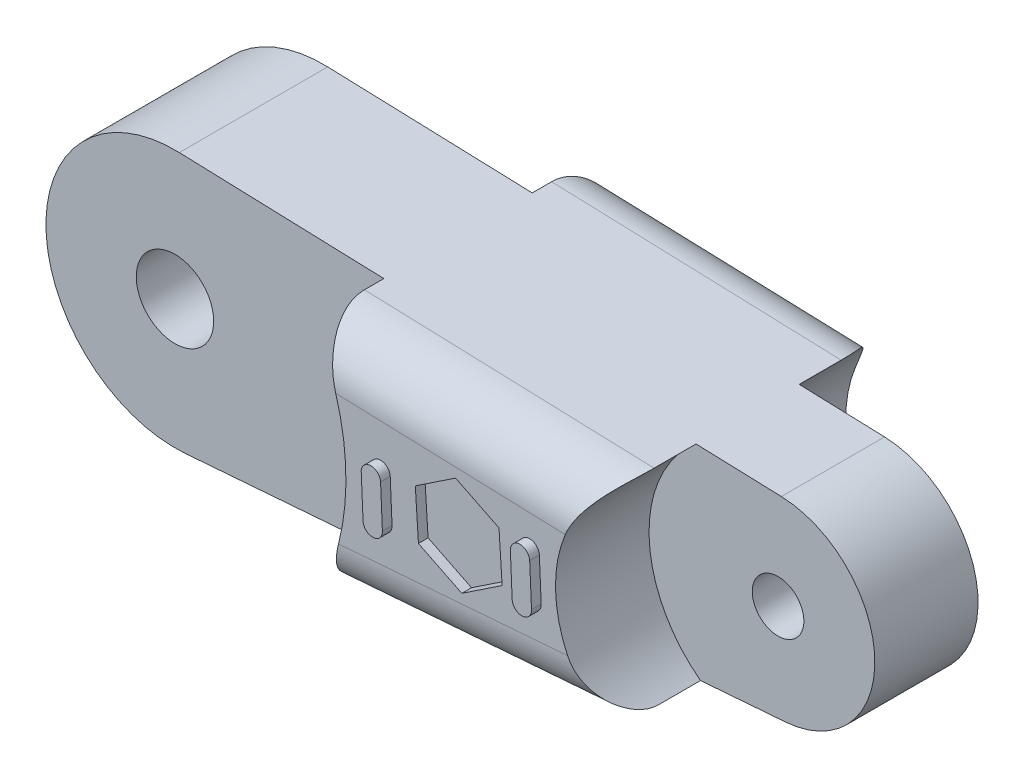
SolidWorks part; units mm, degrees
ref_plane "Front Plane" through (0, 0, 0) normal (0, 0, 1) x (1, 0, 0)
ref_plane "Top Plane" through (0, 0, 0) normal (0, 1, 0) x (1, 0, 0)
ref_plane "Right Plane" through (0, 0, 0) normal (1, 0, 0) x (0, 0, -1)
sketch "Sketch1" plane through (0, 0, 0) normal (0, 1, 0) x (1, 0, 0)
  line L0 (-91.1353, -13.0139) -> (-1.5416, -19.9405)
  line L1 (-90.4891, 16.9328) -> (-0.6801, 19.9884)
  arc A0 (-1.5416, -19.9405) -> (-0.6801, 19.9884) centre (0, 0) ccw
  arc A1 (-90.4891, 16.9328) -> (-91.1353, -13.0139) centre (-89.9791, 1.9414) ccw
  dimension "D2" = 30
  dimension "D3" = 40
  dimension "D1" = 90
extrude "Boss-Extrude1" add sketch "Sketch1" along normal mid plane 45
sketch "Sketch2" plane through (0, -22.5, 0) normal (0, -1, 0) x (1, 0, 0)
  circle A0 centre (0, 0) radius 37.5
  circle A1 centre (-89.9791, -1.9414) radius 20
  dimension "D1" = 40
  dimension "D2" = 75
extrude "Cut-Extrude1" cut sketch "Sketch2" against normal blind 11
ref_plane "Plane1" through (0, 0, 0) normal (0, -1, 0) x (-1, 0, 0)
mirror "Mirror1" about plane through (0, 0, 0) normal (0, -1, 0) of "Cut-Extrude1"
fillet "Fillet1" radius 8 4 edges at (-55.5573, 22.5, 15.7645) (-54.8256, 22.5, -18.1462) (-54.8256, -22.5, -18.1462) (-55.5573, -22.5, 15.7645)
sketch "Sketch4" plane through (0, -11.5, 0) normal (0, -1, 0) x (1, 0, 0)
  circle A0 centre (0, 0) radius 6
  circle A1 centre (-89.9791, -1.9414) radius 4
  dimension "D1" = 12
  dimension "D2" = 8
extrude "Cut-Extrude2" cut sketch "Sketch4" against normal blind 40
sketch "Sketch5" plane through (0, 22.5, 0) normal (0, 1, 0) x (1, 0, 0)
  line L0 (-89.9791, 1.9414) -> (0, 0) construction
  line L2 (-61.5566, 4.8014) -> (-61.3986, -2.7025)
  line L3 (-61.3986, -2.7025) -> (-54.821, -6.3176)
  line L4 (-54.821, -6.3176) -> (-48.4015, -2.4288)
  line L5 (-48.4015, -2.4288) -> (-48.5595, 5.0751)
  line L6 (-48.5595, 5.0751) -> (-55.1371, 8.6902)
  line L7 (-55.1371, 8.6902) -> (-61.5566, 4.8014)
  circle A0 centre (-54.9791, 1.1863) radius 6.5 construction
  point P0 (-89.9791, 1.9414)
  point P1 (0, 0)
  point P9 (-48.4805, 1.3231)
  dimension "D1" = 13
  dimension "D2" = 35
extrude "Cut-Extrude3" cut sketch "Sketch5" against normal blind 1.5
sketch "Sketch6" plane through (0, 22.5, 0) normal (0, 1, 0) x (1, 0, 0)
  line L0 (-89.9791, 1.9414) -> (0, 0) construction
  line L1 (-66.1277, -1.9195) -> (-66.1277, 4.5371) construction
  line L2 (-67.6277, -1.9195) -> (-67.6277, 4.5371)
  line L3 (-64.6277, -1.9195) -> (-64.6277, 4.5371)
  line L4 (-42.9913, -1.9195) -> (-42.9913, 4.5371) construction
  line L5 (-44.4913, -1.9195) -> (-44.4913, 4.5371)
  line L6 (-41.4913, -1.9195) -> (-41.4913, 4.5371)
  arc A0 (-77.9459, -14.0336) -> (-77.268, 17.3826) centre (-89.9791, 1.9414) ccw construction
  arc A1 (-35.9157, 10.7849) -> (-36.3474, -9.2258) centre (0, 0) ccw construction
  arc A2 (-67.6277, -1.9195) -> (-64.6277, -1.9195) centre (-66.1277, -1.9195) ccw
  arc A3 (-64.6277, 4.5371) -> (-67.6277, 4.5371) centre (-66.1277, 4.5371) ccw
  arc A4 (-44.4913, -1.9195) -> (-41.4913, -1.9195) centre (-42.9913, -1.9195) ccw
  arc A5 (-41.4913, 4.5371) -> (-44.4913, 4.5371) centre (-42.9913, 4.5371) ccw
  point P0 (-89.9791, 1.9414)
  point P1 (0, 0)
  point P7 (-69.9837, 1.51)
  point P8 (-61.4837, 1.3266)
  point P12 (-48.4913, 1.0463)
  point P13 (-37.4913, 0.8089)
  point P19 (-66.1277, 1.3088)
  point P24 (-42.9913, 1.3088)
  dimension "D1" = 8.5
  dimension "D2" = 11
  dimension "D3" = 3
  dimension "D4" = 3
  dimension "D5" = 3.856
  dimension "D6" = 5.5
extrude "Boss-Extrude2" add sketch "Sketch6" along normal blind 1.5
mirror "Mirror2" about plane through (0, 0, 0) normal (0, -1, 0) of "Boss-Extrude2", "Cut-Extrude3"
sketch "Sketch7" plane through (0, -11.5, 0) normal (0, -1, 0) x (1, 0, 0)
  circle A0 centre (-89.9791, -1.9414) radius 20
extrude "Cut-Extrude4" cut sketch "Sketch7" against normal blind 3.5
mirror "Mirror3" about plane through (0, 0, 0) normal (0, 1, 0) of "Cut-Extrude4"
sketch "Sketch8" plane through (0, 0, 0) normal (0, 1, 0) x (1, 0, 0)
  point P0 (-89.9791, 1.9414)
move or copy body "Body-Move/Copy1" bodies to move or copy 109 copy no translate (89.9791, 0, 1.9414)
move or copy body "Body-Move/Copy7" bodies to move or copy 110 copy no rotation origin (0, 0, 0) rotation axis (-0.0154, -0.707, 0.707) rotation angle 178.232
move or copy body "Body-Move/Copy8" bodies to move or copy 116 copy no rotation origin (0, 0, 0) rotation axis (0, 0, -1) rotation angle 1.26
move or copy body "Body-Move/Copy9" bodies to move or copy 117 copy no rotation origin (0, 0, 0) rotation axis (0, 0, 1) rotation angle 1.26
move or copy body "Body-Move/Copy10" bodies to move or copy 118 copy no rotation origin (0, 0, 0) rotation axis (1, 0, 0) rotation angle 180
